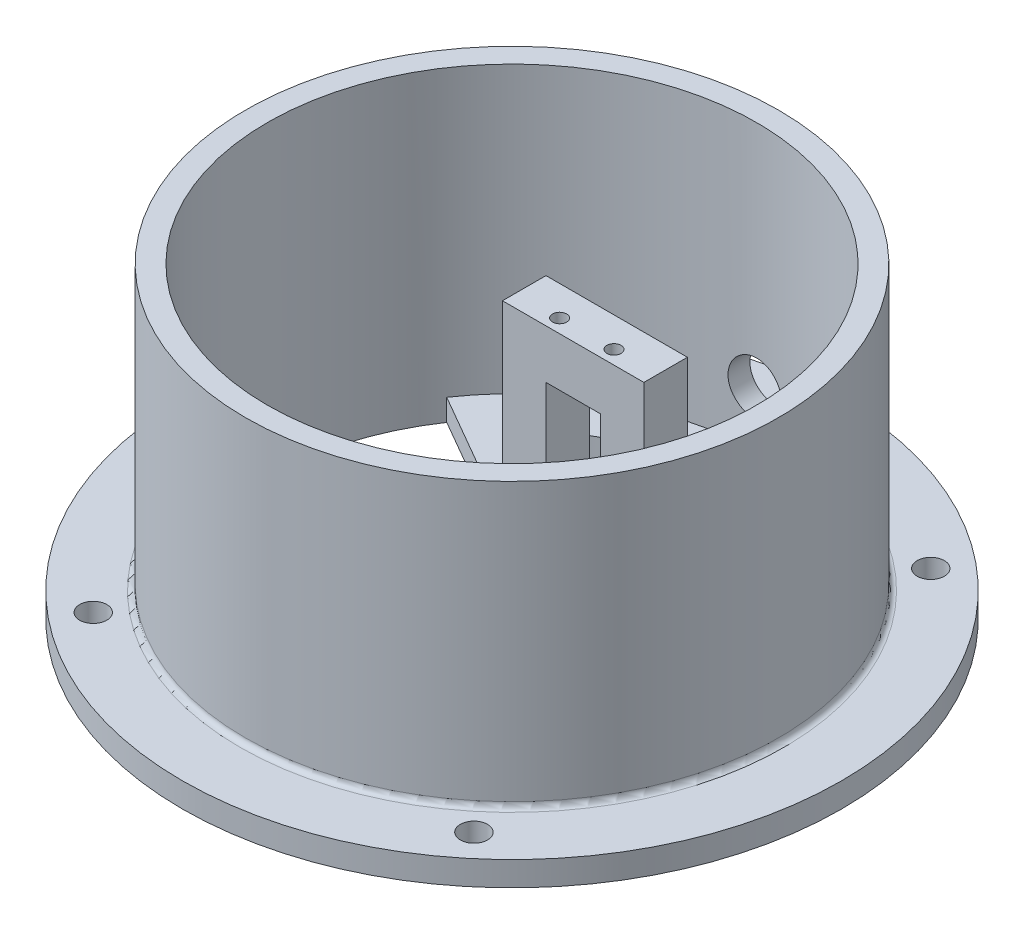
SolidWorks part; units mm, degrees
ref_plane "Front Plane" through (0, 0, 0) normal (0, 0, 1) x (1, 0, 0)
ref_plane "Top Plane" through (0, 0, 0) normal (0, 1, 0) x (1, 0, 0)
ref_plane "Right Plane" through (0, 0, 0) normal (1, 0, 0) x (0, 0, -1)
sketch "Sketch2" plane through (0, 0, 0) normal (0, 1, 0) x (1, 0, 0)
  circle A0 centre (0, 0) radius 60.625
  circle A1 centre (0, 0) radius 45
  dimension "D1" = 121.25
  dimension "D2" = 90
extrude "Boss-Extrude1" add sketch "Sketch2" along normal blind 4.5
sketch "Sketch3" plane through (0, 4.5, 0) normal (0, 1, 0) x (1, 0, 0)
  circle A2 centre (0, 0) radius 45 construction
  circle A4 centre (0, 0) radius 49
  circle A5 centre (0, 0) radius 49
  circle A6 centre (0, 0) radius 45
  dimension "D1" = 4
extrude "Boss-Extrude2" add sketch "Sketch3" along normal blind 52
sketch "Sketch4" plane through (0, 0, 0) normal (1, 0, 0) x (0, 0, -1)
  line L0 (-46.75, 38.5) -> (-31.75, 38.5)
  line L1 (-31.75, 38.5) -> (-31.75, 30.5)
  line L2 (-31.75, 30.5) -> (-46.75, 30.5)
  line L3 (-46.75, 30.5) -> (-46.75, 38.5)
  line L4 (-45, 56.5) -> (-45, 0)
  line L5 (-31.75, 30.5) -> (-45, 17.25)
  line L6 (-45, 0) -> (45, 0) construction
  line L7 (11.25, 38.5) -> (19.25, 38.5)
  line L8 (11.25, 38.5) -> (11.25, 0)
  line L9 (11.25, 0) -> (19.25, 0)
  line L10 (19.25, 38.5) -> (19.25, 0)
  line L11 (11.25, 38.5) -> (19.25, 0) construction
  line L12 (11.25, 0) -> (19.25, 38.5) construction
  line L13 (49, 56.5) -> (-49, 56.5) construction
  line L14 (45, 56.5) -> (-45, 56.5) construction
  point P8 (15.25, 19.25)
  dimension "D1" = 8
  dimension "D2" = 18
  dimension "D3" = 11.25
  dimension "D4" = 43
  dimension "D5" = 15
  dimension "D6" = 8
  dimension "D7" = 45
  dimension "D8" = 18
extrude "Boss-Extrude3" add sketch "Sketch4" along normal mid plane 26 contours L5 L2 L4 | L0 L4 L2 L1 | L10 L7 L8 L9
sketch "Sketch5" plane through (0, 0, 0) normal (0, 0, 1) x (1, 0, 0)
  line L6 (-5, 29.5) -> (5, 29.5)
  line L7 (-5, 29.5) -> (-5, 9.5)
  line L9 (5, 29.5) -> (5, 9.5)
  line L10 (-5, 29.5) -> (5, 9.5) construction
  line L11 (-5, 9.5) -> (5, 29.5) construction
  line L12 (13, 38.5) -> (-13, 38.5) construction
  line L14 (5, 9.5) -> (-5, 9.5)
  line L15 (49, 4.5) -> (-49, 4.5) construction
  point P0 (0, 19.5)
  point P5 (0, 9.5)
  dimension "D1" = 10
  dimension "D2" = 9
  dimension "D3" = 5
extrude "Cut-Extrude1" cut sketch "Sketch5" against normal blind 26
sketch "Sketch6" plane through (0, 0, -11.25) normal (0, 0, 1) x (1, 0, 0)
  line L0 (-60.625, 0) -> (60.625, 0) construction
  circle A0 centre (0, 14) radius 5
  dimension "D1" = 10
  dimension "D2" = 14
extrude "Cut-Extrude2" cut sketch "Sketch6" against normal through all
sketch "Sketch7" plane through (0, 38.5, 0) normal (0, 1, 0) x (1, 0, 0)
  line L0 (-5, -34.25) -> (5, -34.25) construction
  line L1 (-5, 13.75) -> (5, 13.75) construction
  line L2 (13, -31.75) -> (-13, -31.75) construction
  circle A0 centre (-5, 13.75) radius 1.3
  circle A1 centre (5, 13.75) radius 1.3
  circle A2 centre (-5, -34.25) radius 1.3
  circle A3 centre (5, -34.25) radius 1.3
  dimension "D1" = 2.6
  dimension "D2" = 5
  dimension "D3" = 10
  dimension "D4" = 10
  dimension "D5" = 2.5
  dimension "D6" = 48
extrude "Cut-Extrude3" cut sketch "Sketch7" against normal blind 7.2
sketch "Sketch8" plane through (0, 0, 0) normal (0, -1, 0) x (1, 0, 0)
  line L0 (13, -11.25) -> (-13, -11.25) construction
  line L1 (13, -11.25) -> (-13, -11.25)
  line L2 (-13, -11.25) -> (-37.2484, -25.2498)
  line L3 (0, 0) -> (0, -45) construction
  line L4 (13, -11.25) -> (37.2484, -25.2498)
  line L5 (-19.5167, -24.25) -> (-24.9065, -27.3618)
  line L6 (19.5167, -24.25) -> (24.9065, -27.3618)
  line L8 (-19.5167, -24.25) -> (19.5167, -24.25)
  line L9 (-10.8564, -19.25) -> (-24.9065, -27.3618) construction
  line L10 (10.8564, -19.25) -> (-10.8564, -19.25) construction
  line L11 (10.8564, -19.25) -> (24.9065, -27.3618) construction
  line L12 (13, -19.25) -> (-13, -19.25) construction
  circle A0 centre (0, 0) radius 45 construction
  arc A1 (-37.2484, -25.2498) -> (37.2484, -25.2498) centre (0, 0) ccw
  arc A2 (-24.9065, -27.3618) -> (24.9065, -27.3618) centre (0, 0) ccw
  dimension "D1" = 60
  dimension "D3" = 5
  dimension "D2" = 8
extrude "Boss-Extrude4" add sketch "Sketch8" against normal blind 4
sketch "Sketch9" plane through (0, 4.5, 0) normal (0, 1, 0) x (1, 0, 0)
  line L1 (-35, 42) -> (35, 42) construction
  line L2 (-35, 42) -> (-35, -42) construction
  line L3 (-35, -42) -> (35, -42) construction
  line L4 (35, 42) -> (35, -42) construction
  line L5 (-35, 42) -> (35, -42) construction
  line L6 (-35, -42) -> (35, 42) construction
  circle A0 centre (35, 42) radius 2.5
  circle A1 centre (35, -42) radius 2.5
  circle A2 centre (-35, -42) radius 2.5
  circle A3 centre (-35, 42) radius 2.5
  point P0 (0, 0)
  dimension "D3" = 5
  dimension "D4" = 5
  dimension "D5" = 5
  dimension "D6" = 5
  dimension "D1" = 84
  dimension "D2" = 70
hole_wizard "CSK for M3 Countersunk Flat Head Screw1" positions "3DSketch1" profile "Sketch10" countersink size "M3" standard "DIN"
sketch3d "3DSketch1"
  point P0 (-35, 4.5, -42)
  point P3 (35, 4.5, -42)
  point P6 (35, 4.5, 42)
  point P9 (-35, 4.5, 42)
sketch "Sketch10" plane through (-35, 4.5, -42) normal (1, 0, 0) x (0, 0, 1)
  line L0 (0, 0) -> (0, 45.4715)
  line L1 (0, 45.4715) -> (1.7, 44.45)
  line L2 (1.7, 44.45) -> (1.7, 1.45)
  line L3 (1.7, 1.45) -> (3.15, 0)
  line L5 (3.15, 0) -> (0, 0)
  line L6 (-1.7, 1.45) -> (-3.15, 0) construction
  line L10 (0, 45.4715) -> (-1.7, 44.45) construction
  line L11 (0, -6.35) -> (0, 107.95) construction
  dimension "Hole Dia." = 3.4
  dimension "Hole Depth" = 44.45
  dimension "Near C'Sink Dia." = 6.3
  dimension "Near C'Sink Angle" = 90
  dimension "Drill Angle" = 118
fillet "Fillet1" radius 1 1 edges at (0, 4.5, 49)
extrude "Cut-Extrude4" cut sketch "Sketch9" against normal through all
